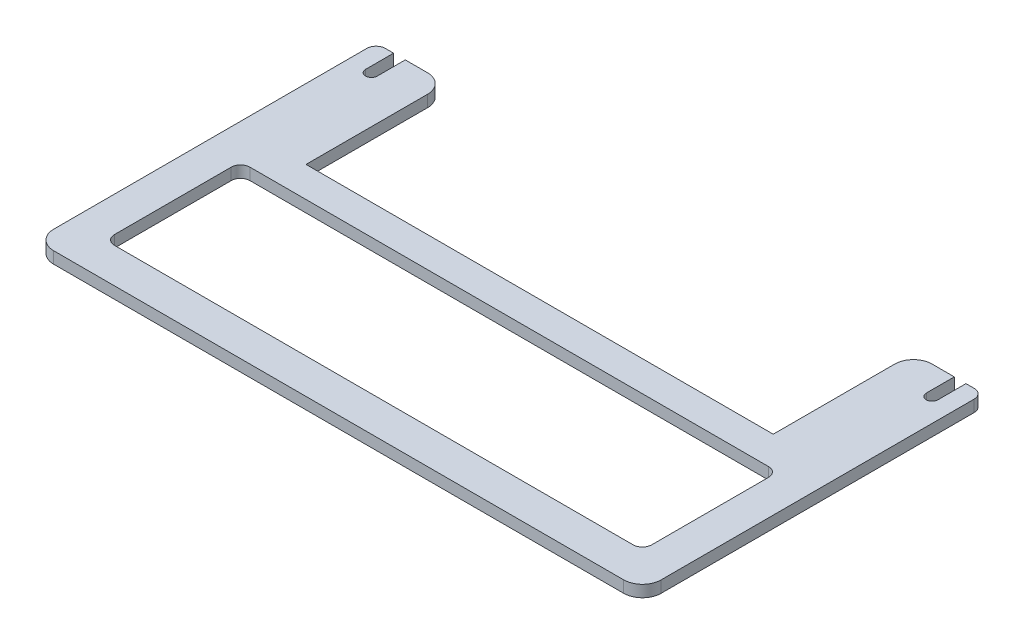
SolidWorks part; units mm, degrees
ref_plane "Front Plane" through (0, 0, 0) normal (0, 0, 1) x (1, 0, 0)
ref_plane "Top Plane" through (0, 0, 0) normal (0, 1, 0) x (1, 0, 0)
ref_plane "Right Plane" through (0, 0, 0) normal (1, 0, 0) x (0, 0, -1)
sketch "Sketch1" plane through (0, 0, 0) normal (0, 1, 0) x (1, 0, 0)
  line L1 (0, 0) -> (177.8, 0)
  line L2 (0, 0) -> (0, 67.31)
  line L3 (0, 67.31) -> (177.8, 67.31)
  line L4 (177.8, 0) -> (177.8, 67.31)
  dimension "D1" = 177.8
  dimension "D2" = 67.31
extrude "Boss-Extrude1" add sketch "Sketch1" along normal blind 3.175
sketch "Sketch3" plane through (0, 3.175, 0) normal (0, 1, 0) x (1, 0, 0)
  line L0 (88.9, 67.31) -> (88.9, 0) construction
  line L1 (177.8, 67.31) -> (0, 67.31) construction
  line L2 (0, 0) -> (177.8, 0) construction
  line L3 (88.9, 46.355) -> (27.9437, 9.525)
  line L4 (27.9437, 9.525) -> (149.8563, 9.525)
  line L5 (9.525, 46.355) -> (9.525, 9.525)
  line L6 (9.525, 9.525) -> (70.4813, 46.355)
  line L7 (70.4813, 46.355) -> (9.525, 46.355)
  line L8 (0, 67.31) -> (0, 0) construction
  line L9 (88.9, 46.355) -> (149.8563, 9.525)
  line L10 (168.275, 9.525) -> (107.3187, 46.355)
  line L11 (107.3187, 46.355) -> (168.275, 46.355)
  line L12 (168.275, 46.355) -> (168.275, 9.525)
  point P6 (12.7, 62.23)
  point P7 (165.1, 62.23)
  point P17 (88.9, 9.525)
  dimension "D1" = 152.4
  dimension "D2" = 5.08
  dimension "D3" = 9.525
  dimension "D4" = 9.525
  dimension "D5" = 9.525
  dimension "D6" = 15.875
sketch "Sketch4" plane through (0, 3.175, 0) normal (0, 1, 0) x (1, 0, 0)
  line L0 (11.1125, 67.31) -> (11.1125, 62.23)
  line L1 (177.8, 67.31) -> (0, 67.31) construction
  line L2 (14.2875, 62.23) -> (14.2875, 67.31)
  line L3 (11.1125, 67.31) -> (14.2875, 67.31)
  line L4 (88.9, 67.31) -> (88.9, 47.4197) construction
  line L5 (88.9, 67.31) -> (88.9, 0) construction
  line L6 (166.6875, 67.31) -> (166.6875, 62.23)
  line L7 (163.5125, 62.23) -> (163.5125, 67.31)
  line L8 (166.6875, 67.31) -> (163.5125, 67.31)
  arc A0 (11.1125, 62.23) -> (14.2875, 62.23) centre (12.7, 62.23) ccw
  arc A1 (166.6875, 62.23) -> (163.5125, 62.23) centre (165.1, 62.23) cw
  dimension "D1" = 3.175
extrude "Cut-Extrude2" cut sketch "Sketch4" against normal through all
sketch "Sketch5" plane through (0, 3.175, 0) normal (0, 1, 0) x (1, 0, 0)
  line L0 (25.4, 67.31) -> (25.4, 54.61)
  line L1 (163.5125, 67.31) -> (14.2875, 67.31) construction
  line L2 (25.4, 54.61) -> (152.4, 54.61)
  line L3 (152.4, 54.61) -> (152.4, 67.31)
  line L4 (152.4, 67.31) -> (25.4, 67.31)
  line L7 (88.9, 67.31) -> (88.9, 90.0705) construction
  dimension "D1" = 12.7
  dimension "D2" = 12.7
extrude "Cut-Extrude3" cut sketch "Sketch5" against normal through all
sketch "Sketch6" plane through (0, 3.175, 0) normal (0, 1, 0) x (1, 0, 0)
  line L0 (0, 54.61) -> (177.8, 54.61) construction
  line L1 (0, 67.31) -> (0, 0) construction
  line L2 (177.8, 0) -> (177.8, 67.31) construction
sketch "Sketch7" plane through (0, 3.175, 0) normal (0, 1, 0) x (1, 0, 0)
  line L0 (0, 54.61) -> (177.8, 54.61) construction
  line L1 (0, 54.61) -> (25.4, 54.61)
  line L2 (0, 54.61) -> (0, 92.71)
  line L3 (0, 92.71) -> (25.4, 92.71)
  line L4 (25.4, 54.61) -> (25.4, 92.71)
  line L5 (152.4, 54.61) -> (177.8, 54.61)
  line L6 (152.4, 54.61) -> (152.4, 92.71)
  line L7 (152.4, 92.71) -> (177.8, 92.71)
  line L8 (177.8, 54.61) -> (177.8, 92.71)
  line L9 (25.4, 67.31) -> (25.4, 54.61) construction
  dimension "D1" = 38.1
extrude "Boss-Extrude2" add sketch "Sketch7" against normal up to surface (3.175 mm away) up to face at (88.9, 0, -55.8403)
sketch "Sketch8" plane through (0, 3.175, 0) normal (0, 1, 0) x (1, 0, 0)
  line L0 (88.9, 54.61) -> (88.9, 78.7147) construction
  line L1 (0, 54.61) -> (177.8, 54.61) construction
  line L2 (25.4, 92.71) -> (0, 92.71) construction
  line L3 (11.1125, 92.71) -> (11.1125, 85.09)
  line L4 (14.2875, 85.09) -> (14.2875, 92.71)
  line L5 (14.2875, 92.71) -> (11.1125, 92.71)
  line L6 (163.5125, 85.09) -> (163.5125, 92.71)
  line L7 (163.5125, 92.71) -> (166.6875, 92.71)
  line L8 (166.6875, 92.71) -> (166.6875, 85.09)
  arc A0 (11.1125, 85.09) -> (14.2875, 85.09) centre (12.7, 85.09) ccw
  arc A1 (166.6875, 85.09) -> (163.5125, 85.09) centre (165.1, 85.09) cw
  point P0 (12.7, 85.09)
  dimension "D1" = 7.62
  dimension "D2" = 3.175
extrude "Cut-Extrude4" cut sketch "Sketch8" against normal through all
fillet "Fillet3" radius 5.08 4 edges at (177.8, 1.5875, -92.71) (152.4, 1.5875, -92.71) (25.4, 1.5875, -92.71) (0, 1.5875, -92.71)
sketch "Sketch9" plane through (0, 3.175, 0) normal (0, 1, 0) x (1, 0, 0)
  line L0 (11.1125, 92.71) -> (5.08, 92.71) construction
  line L1 (0, 0) -> (6.35, 0)
  line L2 (0, 0) -> (0, 92.71)
  line L3 (0, 92.71) -> (6.35, 92.71)
  line L4 (6.35, 0) -> (6.35, 92.71)
  line L6 (177.8, 0) -> (171.45, 0)
  line L7 (177.8, 0) -> (177.8, 92.71)
  line L8 (177.8, 92.71) -> (171.45, 92.71)
  line L9 (171.45, 0) -> (171.45, 92.71)
  line L10 (172.72, 92.71) -> (166.6875, 92.71) construction
  dimension "D1" = 6.35
  dimension "D2" = 6.35
extrude "Cut-Extrude5" cut sketch "Sketch9" against normal through all
fillet "Fillet4" radius 2.54 2 edges at (171.45, 1.5875, -92.71) (6.35, 1.5875, -92.71)
fillet "Fillet5" radius 5.08 2 edges at (171.45, 1.5875, 0) (6.35, 1.5875, 0)
sketch "Sketch10" plane through (0, 3.175, 0) normal (0, 1, 0) x (1, 0, 0)
  line L0 (25.4, 54.61) -> (152.4, 54.61) construction
  line L1 (15.875, 46.355) -> (161.925, 46.355)
  line L2 (15.875, 46.355) -> (15.875, 9.525)
  line L3 (15.875, 9.525) -> (161.925, 9.525)
  line L4 (161.925, 46.355) -> (161.925, 9.525)
  line L5 (11.43, 0) -> (166.37, 0) construction
  line L6 (6.35, 5.08) -> (6.35, 90.17) construction
  line L7 (171.45, 90.17) -> (171.45, 5.08) construction
  dimension "D1" = 8.255
  dimension "D2" = 9.525
  dimension "D3" = 9.525
  dimension "D4" = 9.525
extrude "Cut-Extrude6" cut sketch "Sketch10" against normal through all
fillet "Fillet6" radius 2.54 4 edges at (161.925, 1.5875, -46.355) (161.925, 1.5875, -9.525) (15.875, 1.5875, -46.355) (15.875, 1.5875, -9.525)
